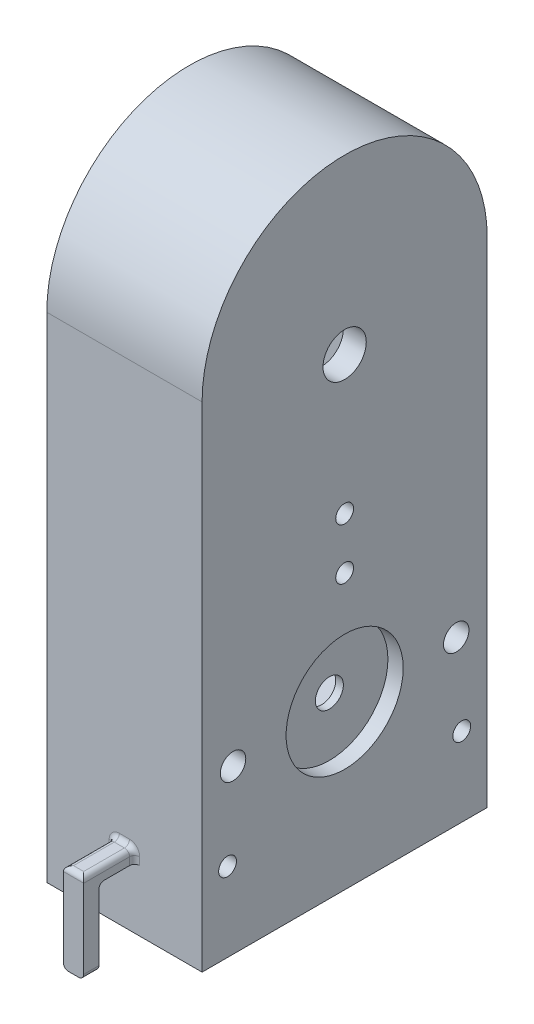
SolidWorks part; units mm, degrees
ref_plane "Front Plane" through (0, 0, 0) normal (0, 0, 1) x (1, 0, 0)
ref_plane "Top Plane" through (0, 0, 0) normal (0, 1, 0) x (1, 0, 0)
ref_plane "Right Plane" through (0, 0, 0) normal (1, 0, 0) x (0, 0, -1)
sketch "Sketch2" plane through (0, 0, 0) normal (0, 1, 0) x (1, 0, 0)
  line L1 (0, 0) -> (30.5, 0)
  line L2 (0, 0) -> (0, -56)
  line L3 (0, -56) -> (30.5, -56)
  line L4 (30.5, 0) -> (30.5, -56)
  arc A6 (30.5, 0) -> (0, 0) centre (15.25, 0) ccw
  dimension "D1" = 30.5
  dimension "D2" = 56
extrude "Boss-Extrude3" add sketch "Sketch2" along normal blind 85
sketch "Sketch4" plane through (30.5, 0, 0) normal (1, 0, 0) x (0, 0, -1)
  line L0 (0, 85) -> (-56, 85) construction
  line L1 (-56, 85) -> (0, 85)
  arc A0 (0, 85) -> (-56, 85) centre (-28, 85) ccw
extrude "Boss-Extrude4" add sketch "Sketch4" against normal blind 30.5
sketch "Sketch3" plane through (0, 0, 0) normal (-1, 0, 0) x (0, 0, 1)
  line L0 (5, 10) -> (5, 80)
  line L11 (5, 80) -> (5, 85)
  line L12 (51, 80) -> (51, 10)
  line L14 (51, 85) -> (51, 80)
  line L17 (5, 10) -> (5, 7)
  line L18 (5, 7) -> (51, 7)
  line L19 (51, 7) -> (51, 10)
  arc A3 (51, 85) -> (5, 85) centre (28, 85) ccw
extrude "Cut-Extrude2" cut sketch "Sketch3" against normal blind 26
sketch "Sketch5" plane through (26, 0, 0) normal (-1, 0, 0) x (0, 0, 1)
  line L0 (0, 0) -> (56, 0) construction
  line L1 (0, 85) -> (0, 0) construction
  circle A0 centre (28, 20) radius 2.75
  circle A1 centre (28, 79.06) radius 4.25
  circle A6 centre (28, 52) radius 1.75
  dimension "D1" = 52
  dimension "D2" = 59.06
  dimension "D3" = 28
  dimension "D4" = 79.06
extrude "Cut-Extrude3" cut sketch "Sketch5" against normal blind 10
sketch "Sketch6" plane through (30.5, 0, 0) normal (1, 0, 0) x (0, 0, -1)
  line L0 (-28, 20) -> (-49.92, 20)
  line L1 (-28, 20) -> (-6.08, 20)
  line L2 (-28, 20) -> (-28, 41.92)
  circle A14 centre (-49.92, 20) radius 2.5
  circle A15 centre (-6.08, 20) radius 2.5
  circle A16 centre (-28, 41.92) radius 1.75
  circle A17 centre (-28, 20) radius 11
sketch "Sketch7" plane through (30.5, 0, 0) normal (1, 0, 0) x (0, 0, -1)
  circle A0 centre (-28, 20) radius 11.5
extrude "Cut-Extrude5" cut sketch "Sketch7" against normal blind 3
sketch "Sketch9" plane through (0, 0, 0) normal (-1, 0, 0) x (0, 0, 1)
  line L0 (0, 0) -> (56, 0) construction
  circle A0 centre (5, 3.5) radius 1.75
  circle A1 centre (51, 3.5) radius 1.75
  dimension "D1" = 3.5
  dimension "D2" = 3.5
extrude "Cut-Extrude7" cut sketch "Sketch9" against normal blind 77
extrude "Cut-Extrude8" cut sketch "Sketch6" against normal blind 77 contours A15 | A16 | A14
sketch "Sketch11" plane through (0, 0, 56) normal (0, 0, 1) x (1, 0, 0)
  line L1 (0, 0) -> (30.5, 0) construction
  line L2 (15.25, 2.5) -> (17.25, 2.5)
  line L3 (17.25, 2.5) -> (17.25, 0)
  line L4 (17.25, 0) -> (15.25, 0)
  line L5 (15.25, 0) -> (13.25, 0)
  line L6 (13.25, 0) -> (13.25, 2.5)
  line L7 (13.25, 2.5) -> (15.25, 2.5)
extrude "Boss-Extrude5" add sketch "Sketch11" along normal blind 10
sketch "Sketch12" plane through (0, 0, 0) normal (0, -1, 0) x (1, 0, 0)
  line L0 (17.25, 66) -> (17.25, 56) construction
  line L1 (13.25, 66) -> (17.25, 66)
  line L2 (13.25, 66) -> (13.25, 63)
  line L3 (13.25, 63) -> (17.25, 63)
  line L4 (17.25, 66) -> (17.25, 63)
  dimension "D1" = 3
extrude "Boss-Extrude6" add sketch "Sketch12" along normal blind 15
fillet "Fillet2" radius 1 9 edges at (17.25, -15, 64.5) (13.25, -15, 64.5) (15.25, 2.5, 56) (15.25, 2.5, 66) (17.25, 1.25, 56) (13.25, 1.25, 56) (15.25, 0, 63) (17.25, 2.5, 61) (13.25, 2.5, 61)
sketch "Sketch13" plane through (0, 0, 0) normal (0, -1, 0) x (1, 0, 0)
  line L0 (8.3481, 28.0047) -> (12.4119, 23.9409)
  line L1 (0, 56) -> (30.5, 56)
  line L2 (0, 56) -> (0, 0)
  line L3 (0, 0) -> (30.5, 0)
  line L4 (30.5, 56) -> (30.5, 0)
  line L5 (12.4119, 23.9409) -> (16.6519, 28.1809)
  line L6 (12.5928, 32.24) -> (16.6519, 28.1809)
  arc A1 (8.3481, 28.0047) -> (12.5928, 32.24) centre (12.5881, 28) cw
extrude "Boss-Extrude7" add sketch "Sketch13" along normal blind 12
sketch "Sketch15" plane through (0, -12, 0) normal (0, -1, 0) x (1, 0, 0)
  line L0 (8.3481, 28.0047) -> (12.4119, 23.9409)
  line L1 (12.4119, 23.9409) -> (16.6519, 28.1809)
  line L2 (12.5928, 32.24) -> (16.6519, 28.1809)
  arc A0 (8.3481, 28.0047) -> (12.5928, 32.24) centre (12.5881, 28) cw
extrude "Cut-Extrude9" cut sketch "Sketch15" against normal blind 22
